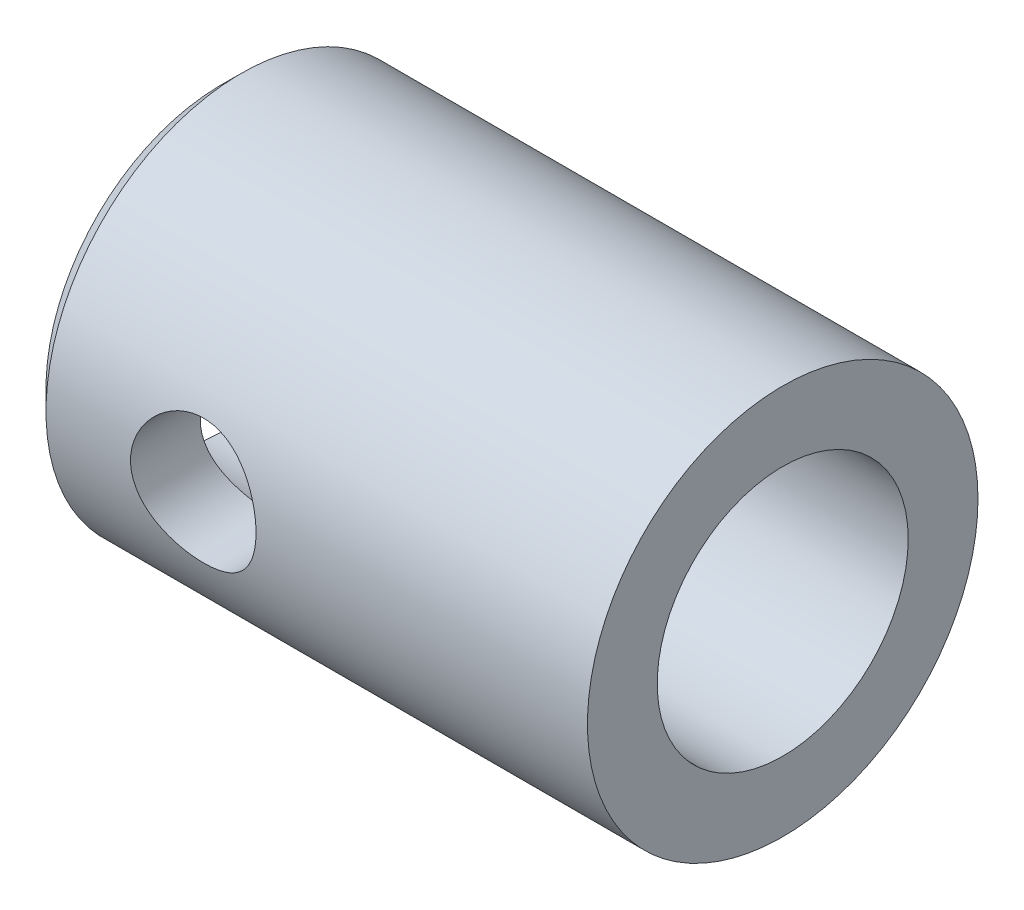
SolidWorks part; units mm, degrees
ref_plane "Front Plane" through (0, 0, 0) normal (0, 0, 1) x (1, 0, 0)
ref_plane "Top Plane" through (0, 0, 0) normal (0, 1, 0) x (1, 0, 0)
ref_plane "Right Plane" through (0, 0, 0) normal (1, 0, 0) x (0, 0, -1)
sketch "Sketch1" plane through (0, 0, 0) normal (1, 0, 0) x (0, 0, -1)
  circle A0 centre (0, 0) radius 14.8209
  dimension "D1" = 29.6418
extrude "Boss-Extrude1" add sketch "Sketch1" along normal blind 42.6212
hole_wizard "Hole1" positions "Sketch3" profile "Sketch4" legacy end condition through all
sketch "Sketch3" plane through (42.6212, 0, 0) normal (1, 0, 0) x (0, 0, -1)
  point P0 (0, 0)
sketch "Sketch4" plane through (42.6212, 0, 0) normal (0, 1, 0) x (0, 0, -1)
  line L0 (0, 0) -> (0, 42.6212)
  line L1 (0, 42.6212) -> (9.525, 42.6212)
  line L2 (9.525, 42.6212) -> (9.525, 0)
  line L3 (9.525, 0) -> (0, 0)
  line L4 (0, 110) -> (0, -10) construction
  dimension "Diameter" = 19.05
  dimension "Depth" = 42.6212
sketch "Sketch23" plane through (42.6212, 0, 0) normal (1, 0, 0) x (0, 0, -1)
  line L0 (0, 0) -> (-14.8209, 0) construction
  circle A0 centre (0, 0) radius 14.8209 construction
  point P5 (0, 0)
  point P6 (0, 0)
  point P7 (0, 0)
hole_wizard "Hole4" positions "3DSketch11" profile "Sketch24" legacy end condition through all
sketch3d "3DSketch11"
  point P0 (12.7, 0, 14.8209)
  point P7 (0, 0, 0)
  dimension "D1" = 12.7
sketch "Sketch24" plane through (12.7, 0, 14.8209) normal (1, 0, 0) x (0, -1, 0)
  line L0 (0, 0) -> (0, 29.6418)
  line L1 (0, 29.6418) -> (4.7625, 29.6418)
  line L2 (4.7625, 29.6418) -> (4.7625, 0)
  line L3 (4.7625, 0) -> (0, 0)
  line L4 (0, 110) -> (0, -10) construction
  dimension "Diameter" = 9.525
  dimension "Depth" = 29.6418
chamfer "Chamfer1" distance 1.524 angle 45 1 edges at (0, 0, -14.8209)
